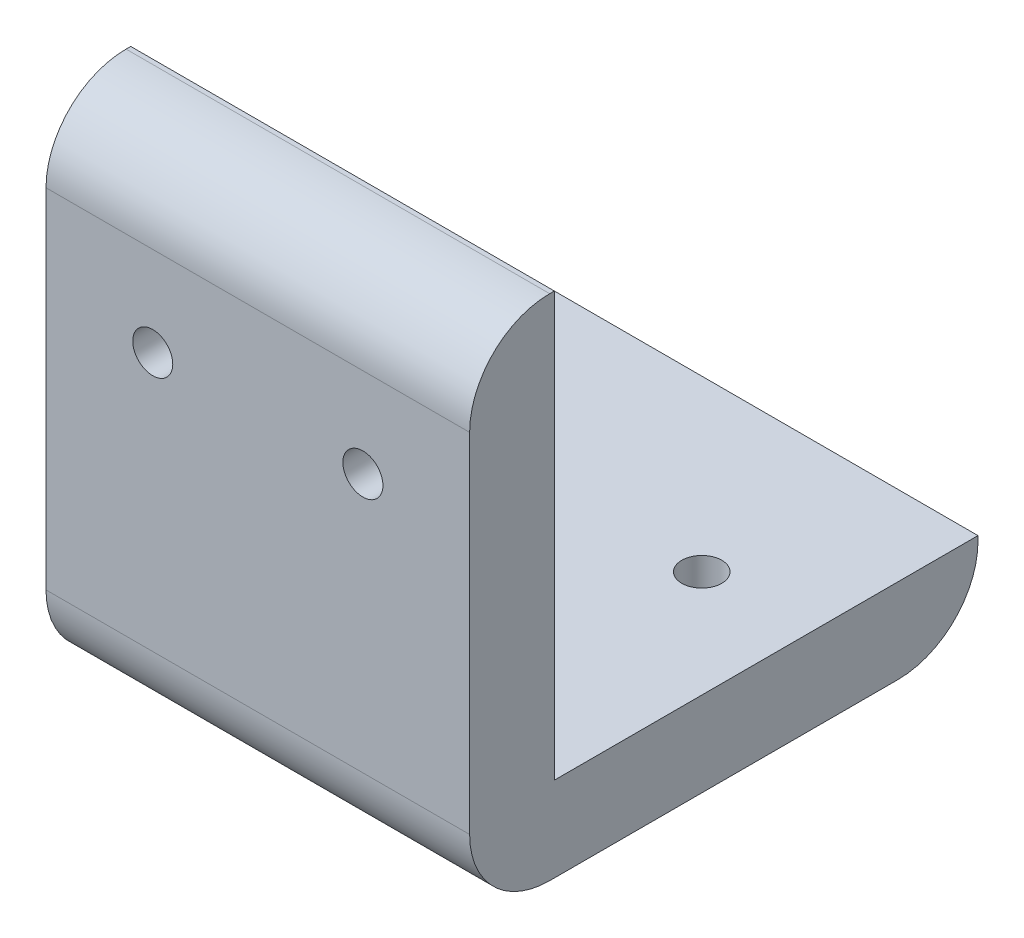
SolidWorks part; units mm, degrees
ref_plane "Front Plane" through (0, 0, 0) normal (0, 0, 1) x (1, 0, 0)
ref_plane "Top Plane" through (0, 0, 0) normal (0, 1, 0) x (1, 0, 0)
ref_plane "Right Plane" through (0, 0, 0) normal (1, 0, 0) x (0, 0, -1)
sketch "Sketch1" plane through (0, 0, 0) normal (1, 0, 0) x (0, 0, -1)
  line L0 (-6.35, 31.75) -> (-6.35, -6.35)
  line L1 (-6.35, -6.35) -> (31.75, -6.35)
  line L2 (31.75, -6.35) -> (31.75, 0)
  line L3 (31.75, 0) -> (0, 0)
  line L4 (0, 0) -> (0, 31.75)
  line L5 (0, 31.75) -> (-6.35, 31.75)
  dimension "D1" = 6.35
  dimension "D2" = 6.35
  dimension "D3" = 31.75
  dimension "D4" = 31.75
extrude "Boss-Extrude1" add sketch "Sketch1" along normal blind 31.75
fillet "Fillet1" radius 6 2 edges at (15.875, 31.75, 6.35) (15.875, -6.35, -31.75)
sketch "Sketch2" plane through (0, 0, 6.35) normal (0, 0, 1) x (1, 0, 0)
  line L0 (8, 19.05) -> (23.75, 19.05) construction
  line L1 (31.75, -6.35) -> (0, -6.35) construction
  line L2 (31.75, 25.75) -> (31.75, -6.35) construction
  circle A0 centre (8, 19.05) radius 1.5
  circle A1 centre (23.75, 19.05) radius 1.5
  point P4 (15.875, 19.05)
  point P7 (15.875, -6.35)
  dimension "D1" = 3
  dimension "D2" = 8
  dimension "D3" = 19.05
extrude "Cut-Extrude1" cut sketch "Sketch2" against normal through all
sketch "Sketch3" plane through (0, -6.35, 0) normal (0, -1, 0) x (1, 0, 0)
  line L0 (8, -19.05) -> (23.75, -19.05) construction
  line L1 (31.75, 6.35) -> (0, 6.35) construction
  line L3 (0, 6.35) -> (0, -25.75) construction
  circle A0 centre (8, -19.05) radius 1.5
  circle A1 centre (23.75, -19.05) radius 1.5
  point P4 (15.875, -19.05)
  point P18 (15.875, 6.35)
  dimension "D1" = 3
  dimension "D2" = 8
  dimension "D3" = 19.05
extrude "Cut-Extrude2" cut sketch "Sketch3" against normal through all
fillet "Fillet2" radius 6 1 edges at (15.875, -6.35, 6.35)
